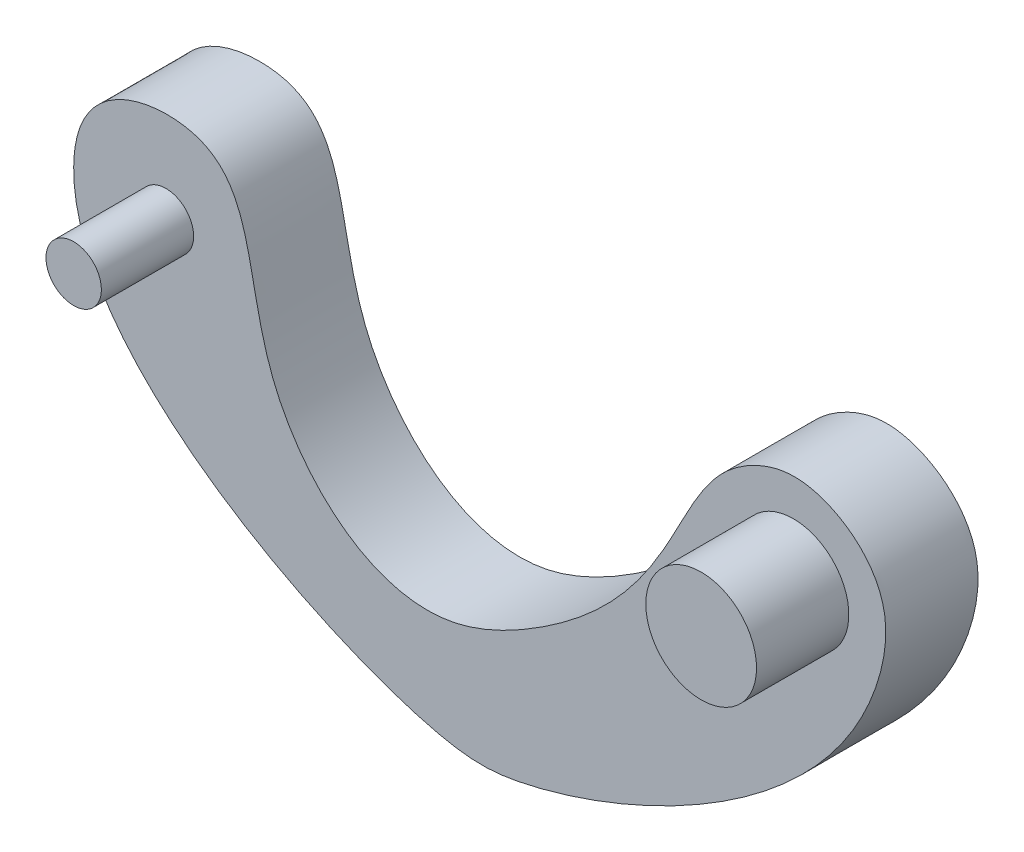
SolidWorks part; units mm, degrees
ref_plane "Alzado" through (0, 0, 0) normal (0, 0, 1) x (1, 0, 0)
ref_plane "Planta" through (0, 0, 0) normal (0, 1, 0) x (1, 0, 0)
ref_plane "Vista lateral" through (0, 0, 0) normal (1, 0, 0) x (0, 0, -1)
sketch "Croquis1" plane through (0, 0, 0) normal (0, 0, 1) x (1, 0, 0)
  spline S0 degree 3 poles (-10.879, 1.7527) (-11.331, -4.2398) (-2.0894, -8.6934) (2.7712, -8.3495) (10.0771, -5.0521) (11.3451, 1.2821) (9.0606, 2.7802) (5.0165, 1.5718) (5.874, -2.2999) (-1.7065, -6.3361) (-4.3544, -4.6633) (-6.4671, -0.8193) (-5.9717, 2.357) (-9.3735, 2.5853) (-10.879, 1.7527) (-11.331, -4.2398) (-2.0894, -8.6934) knots -0.070391 -0.051462 -0.005718 0 0.143874 0.181231 0.352203 0.380711 0.437803 0.471514 0.684113 0.720691 0.800711 0.823924 0.929609 0.948538 0.994282 1 1.143874 1.181231 1.352203 only from (-11, 0) to (-11, 0)
extrude "Saliente-Extruir4" add sketch "Croquis1" along normal blind 2.5
sketch "Croquis4" plane through (0, 0, 2.5) normal (0, 0, 1) x (1, 0, 0)
  circle A0 centre (8.5, 0) radius 1.5
  circle A1 centre (-8.5, 0) radius 0.75
  dimension "D2" = 3
  dimension "D3" = 8.5
  dimension "D4" = 8.5
  dimension "D1" = 1.5
extrude "Saliente-Extruir6" add sketch "Croquis4" along normal blind 2.5
sketch "Croquis5" plane through (0, 0, 0) normal (0, 0, -1) x (-1, 0, 0)
  circle A0 centre (-8.5, 0) radius 0.75
  dimension "D1" = 1.5
extrude "Cortar-Extruir1" cut sketch "Croquis5" against normal blind 2
